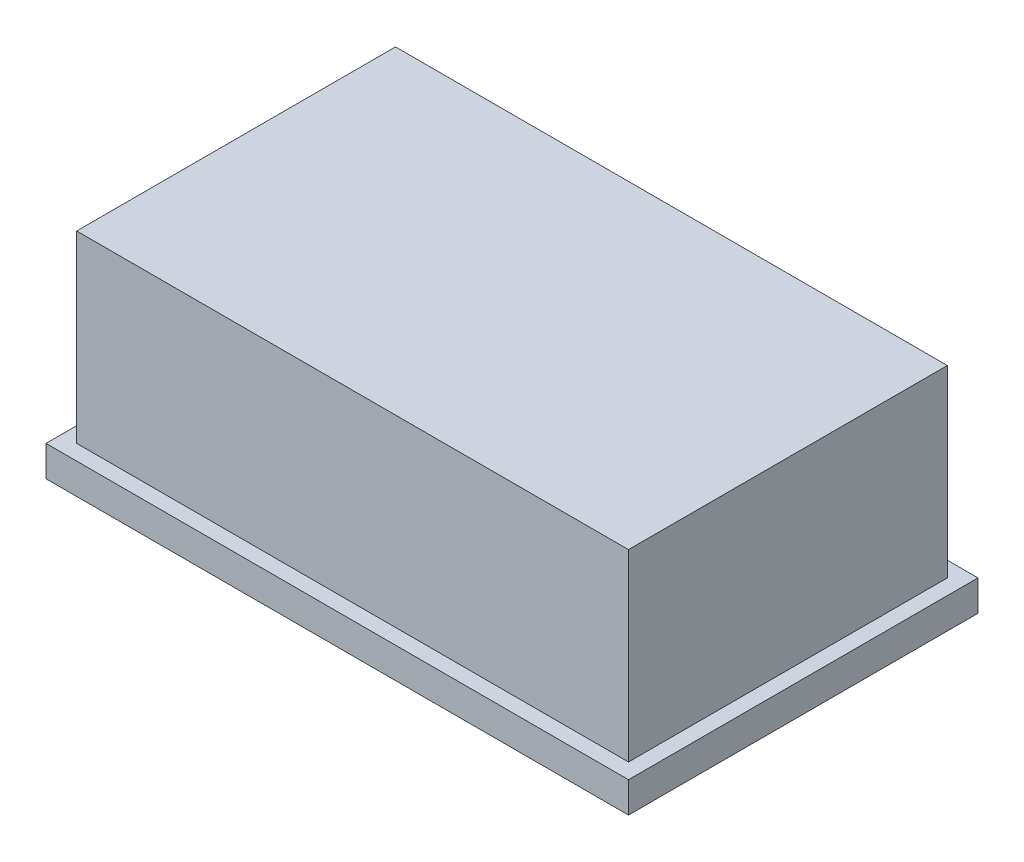
SolidWorks part; units mm, degrees
ref_plane "前视基准面" through (0, 0, 0) normal (0, 0, 1) x (1, 0, 0)
ref_plane "上视基准面" through (0, 0, 0) normal (0, 1, 0) x (1, 0, 0)
ref_plane "右视基准面" through (0, 0, 0) normal (1, 0, 0) x (0, 0, -1)
other "Configuration Table"
sketch "草图1" plane through (0, 0, 0) normal (0, 1, 0) x (1, 0, 0)
  line L1 (0, 0) -> (47.5, 0)
  line L2 (0, 0) -> (0, 28.5)
  line L3 (0, 28.5) -> (47.5, 28.5)
  line L4 (47.5, 0) -> (47.5, 28.5)
  dimension "D1" = 28.5
  dimension "D2" = 47.5
extrude "凸台-拉伸1" add sketch "草图1" along normal blind 2.5
sketch "草图2" plane through (0, 2.5, 0) normal (0, 1, 0) x (1, 0, 0)
  line L0 (0, 14.25) -> (47.5, 14.25) construction
  line L1 (0, 28.5) -> (0, 0) construction
  line L2 (47.5, 0) -> (47.5, 28.5) construction
  line L3 (23.75, 28.5) -> (23.75, 0) construction
  line L4 (47.5, 28.5) -> (0, 28.5) construction
  line L5 (0, 0) -> (47.5, 0) construction
  line L7 (1.25, 1.25) -> (46.25, 1.25)
  line L8 (1.25, 1.25) -> (1.25, 27.25)
  line L9 (1.25, 27.25) -> (46.25, 27.25)
  line L10 (46.25, 1.25) -> (46.25, 27.25)
  line L11 (1.25, 1.25) -> (46.25, 27.25) construction
  line L12 (1.25, 27.25) -> (46.25, 1.25) construction
  point P12 (23.75, 14.25)
  dimension "D1" = 26
  dimension "D2" = 45
extrude "凸台-拉伸2" add sketch "草图2" along normal blind 15
sketch "草图3" plane through (0, 0, 0) normal (0, -1, 0) x (1, 0, 0)
  line L0 (0, -14.25) -> (47.5, -14.25) construction
  line L1 (0, -28.5) -> (0, 0) construction
  line L2 (47.5, 0) -> (47.5, -28.5) construction
  line L3 (23.75, 0) -> (23.75, -14.25) construction
  line L4 (0, 0) -> (47.5, 0) construction
  line L6 (5.75, -23.25) -> (41.75, -23.25)
  line L7 (5.75, -23.25) -> (5.75, -5.25)
  line L8 (5.75, -5.25) -> (41.75, -5.25)
  line L9 (41.75, -23.25) -> (41.75, -5.25)
  line L10 (5.75, -23.25) -> (41.75, -5.25) construction
  line L11 (5.75, -5.25) -> (41.75, -23.25) construction
  dimension "D1" = 18
  dimension "D2" = 36
extrude "切除-拉伸1" cut sketch "草图3" against normal blind 3
chamfer "倒角1" distance 2 angle 45 4 edges at (41.75, 0, -14.25) (23.75, 0, -23.25) (5.75, 0, -14.25) (23.75, 0, -5.25)
